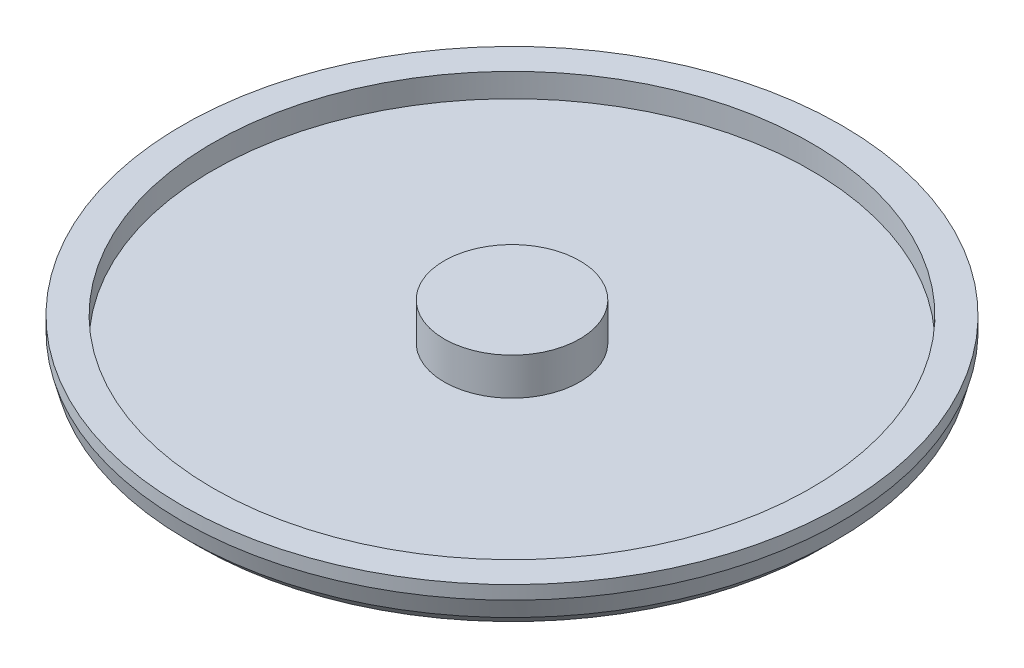
SolidWorks part; units mm, degrees
material "1060 Alloy"
ref_plane "Front Plane" through (0, 0, 0) normal (0, 0, 1) x (1, 0, 0)
ref_plane "Top Plane" through (0, 0, 0) normal (0, 1, 0) x (1, 0, 0)
ref_plane "Right Plane" through (0, 0, 0) normal (1, 0, 0) x (0, 0, -1)
sketch "Sketch1" plane through (0, 0, 0) normal (0, 1, 0) x (1, 0, 0)
  circle A0 centre (0, 0) radius 486.25
  dimension "D1" = 972.5
extrude "Boss-Extrude1" add sketch "Sketch1" along normal blind 65
sketch "Sketch3" plane through (0, 65, 0) normal (0, 1, 0) x (1, 0, 0)
  circle A0 centre (0, 0) radius 441.25
  dimension "D1" = 882.5
extrude "Cut-Extrude1" cut sketch "Sketch3" against normal offset from surface (35 mm away) 30 up to face at (0, 0, 486.25)
ref_axis "Axis1" through (0, 89.25, 0) along (0, -1, 0)
sketch "Sketch5" plane through (0, 0, 0) normal (1, 0, 0) x (0, 0, -1)
  line L0 (486.25, 65) -> (486.25, 45) construction
  line L1 (486.25, 0) -> (486.25, 65) construction
  line L2 (486.25, 45) -> (478.9295, 17.6795)
  line L3 (478.9295, 17.6795) -> (461.25, 0)
  line L4 (-486.25, 0) -> (486.25, 0) construction
  line L5 (461.25, 0) -> (486.25, 0)
  line L6 (486.25, 0) -> (486.25, 45)
  dimension "D1" = 20
  dimension "D2" = 15
  dimension "D3" = 45
  dimension "D4" = 25
revolve "Cut-Revolve1" cut sketch "Sketch5" angle 360 about axis through (0, 89.25, 0) along (0, -1, 0)
sketch "Sketch6" plane through (0, 30, 0) normal (0, 1, 0) x (1, 0, 0)
  circle A0 centre (0, 0) radius 100
  dimension "D1" = 200
extrude "Boss-Extrude3" add sketch "Sketch6" along normal blind 55
equation "\"A\"= 65"
equation "\"B\" = 972.5"
equation "\"D1@Sketch1\"=\"B\""
equation "\"D1@Boss-Extrude1\"=\"A\""
equation "\"D1@Sketch3\"=\"B\"-90"
equation "\"D1@Boss-Extrude3\"=\"A\"+20-30"
